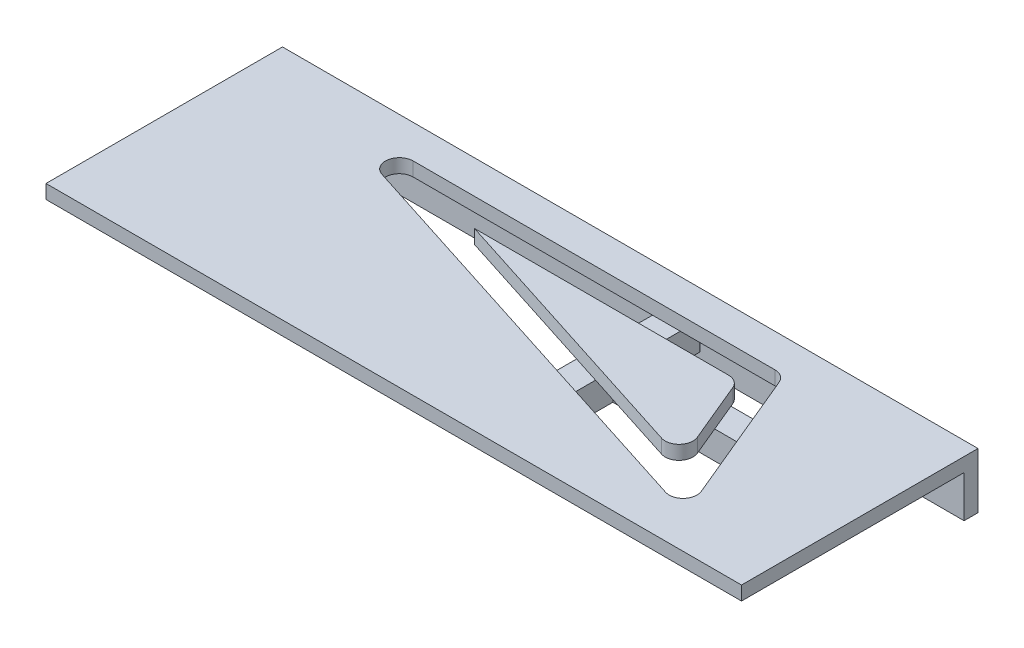
SolidWorks part; units mm, degrees
ref_plane "Front Plane" through (0, 0, 0) normal (0, 0, 1) x (1, 0, 0)
ref_plane "Top Plane" through (0, 0, 0) normal (0, 1, 0) x (1, 0, 0)
ref_plane "Right Plane" through (0, 0, 0) normal (1, 0, 0) x (0, 0, -1)
sketch "Sketch1" plane through (0, 0, 0) normal (0, 0, 1) x (1, 0, 0)
  line L1 (0, 0) -> (250, 0)
  line L2 (0, 0) -> (0, 20)
  line L3 (0, 20) -> (250, 20)
  line L4 (250, 0) -> (250, 20)
  dimension "D1" = 20
  dimension "D2" = 250
extrude "Boss-Extrude1" add sketch "Sketch1" along normal blind 5
sketch "Sketch2" plane through (0, 0, 5) normal (0, 0, 1) x (1, 0, 0)
  line L0 (250, 0) -> (250, 20) construction
  line L1 (0, 20) -> (250, 20)
  line L2 (0, 20) -> (0, 15)
  line L3 (0, 15) -> (250, 15)
  line L4 (250, 20) -> (250, 15)
  dimension "D1" = 5
extrude "Boss-Extrude2" add sketch "Sketch2" along normal blind 80
sketch "Sketch4" plane through (0, 15, 0) normal (0, -1, 0) x (1, 0, 0)
  line L0 (150, 85) -> (150, 36.245) construction
  line L1 (0, 85) -> (250, 85) construction
  line L2 (0, 0) -> (250, 0) construction
  line L3 (0, 85) -> (0, 5) construction
  line L4 (150, 36.245) -> (150, 65.7199) construction
  line L5 (145, 31.245) -> (145, 65.7199)
  line L6 (155, 36.245) -> (155, 65.7199)
  line L7 (150, 31.245) -> (150, 5.1786) construction
  line L8 (155, 26.245) -> (155, 5.1786)
  line L9 (145, 31.245) -> (145, 5.1786)
  line L10 (150, 31.245) -> (214.2862, 31.245) construction
  line L11 (155, 36.245) -> (214.2862, 36.245)
  line L12 (155, 26.245) -> (214.2862, 26.245)
  line L13 (150, 31.245) -> (150, 0) construction
  arc A1 (155, 65.7199) -> (145, 65.7199) centre (150, 65.7199) ccw
  arc A3 (145, 5.1786) -> (155, 5.1786) centre (150, 5.1786) ccw
  arc A5 (214.2862, 26.245) -> (214.2862, 36.245) centre (214.2862, 31.245) ccw
  point P10 (150, 48.4824)
  point P15 (150, 18.2118)
  point P22 (182.1431, 31.245)
  dimension "D2" = 5
  dimension "D3" = 5
  dimension "D4" = 5
  dimension "D1" = 150
extrude "Boss-Extrude3" add sketch "Sketch4" along normal blind 10
sketch "Sketch3" plane through (0, 15, 0) normal (0, -1, 0) x (1, 0, 0)
  line L0 (209, 65) -> (189, 17) construction
  line L1 (189, 17) -> (59, 17) construction
  line L2 (209, 65) -> (59, 17) construction
  line L3 (0, 85) -> (250, 85) construction
  line L4 (207.4761, 69.7621) -> (57.4761, 21.7621)
  line L5 (0, 85) -> (0, 5) construction
  line L6 (189, 12) -> (59, 12)
  line L7 (213.6154, 63.0769) -> (193.6154, 15.0769)
  line L8 (189.9283, 53.6473) -> (91.0305, 22)
  line L9 (182.3333, 22) -> (91.0305, 22)
  line L10 (196.0675, 46.9621) -> (186.9487, 25.0769)
  line L11 (217.7739, 73.0574) -> (26.9695, 12) construction
  line L12 (217.7739, 73.0574) -> (192.3333, 12) construction
  line L13 (192.3333, 12) -> (26.9695, 12) construction
  line L14 (185.6667, 22) -> (91.0305, 22) construction
  line L15 (200.2261, 56.9426) -> (185.6667, 22) construction
  line L16 (200.2261, 56.9426) -> (91.0305, 22) construction
  arc A0 (207.4761, 69.7621) -> (213.6154, 63.0769) centre (209, 65) cw
  arc A1 (189, 12) -> (193.6154, 15.0769) centre (189, 17) ccw
  arc A2 (182.3333, 22) -> (186.9487, 25.0769) centre (182.3333, 27) ccw
  arc A3 (189.9283, 53.6473) -> (196.0675, 46.9621) centre (191.4522, 48.8852) cw
  arc A4 (57.4761, 21.7621) -> (59, 12) centre (59, 17) ccw
  point P5 (0, 0)
  point P7 (40.6507, 91.7862)
  dimension "D8" = 5
  dimension "D1" = 68
  dimension "D2" = 20
  dimension "D3" = 130
  dimension "D4" = 150
  dimension "D5" = 59
  dimension "D6" = 5
  dimension "D7" = 5
extrude "Cut-Extrude2" cut sketch "Sketch3" against normal blind 10
